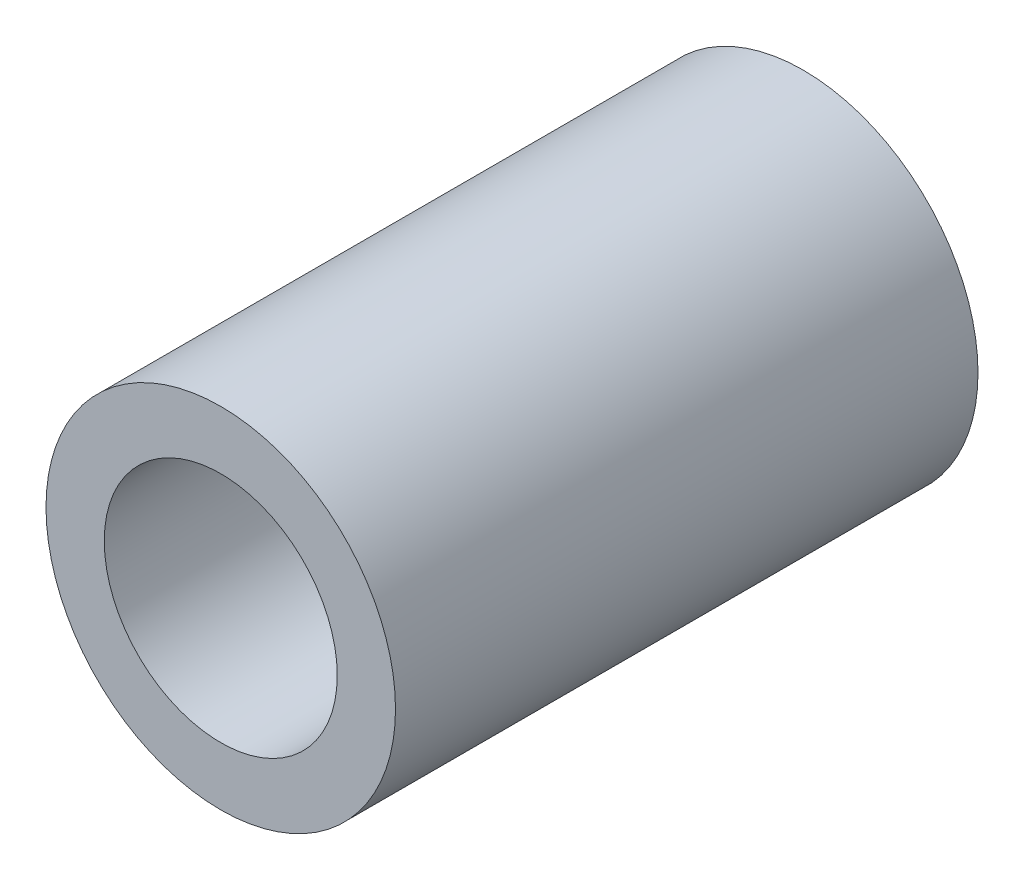
SolidWorks part; units mm, degrees
material "Aluminum Bronze"
ref_plane "Plan de face" through (0, 0, 0) normal (0, 0, 1) x (1, 0, 0)
ref_plane "Plan de dessus" through (0, 0, 0) normal (0, 1, 0) x (1, 0, 0)
ref_plane "Plan de droite" through (0, 0, 0) normal (1, 0, 0) x (0, 0, -1)
sketch "Esquisse1" plane through (0, 0, 0) normal (0, 0, 1) x (1, 0, 0)
  circle A0 centre (0, 0) radius 4
  circle A1 centre (0, 0) radius 6
  dimension "D1" = 8
  dimension "D2" = 2
extrude "Boss.-Extru.1" add sketch "Esquisse1" along normal blind 20
